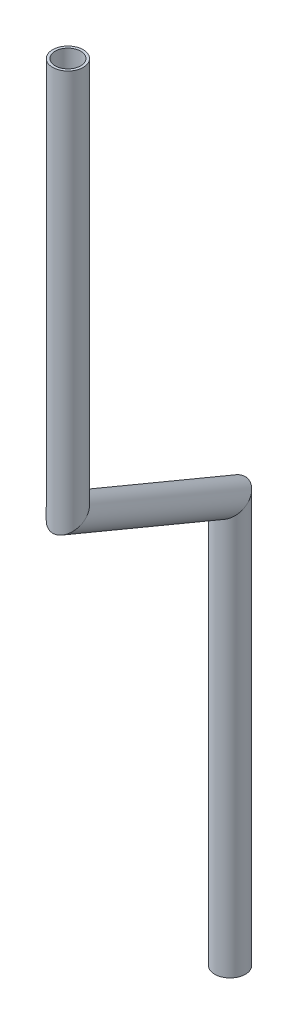
SolidWorks part; units mm, degrees
ref_plane "Front Plane" through (0, 0, 0) normal (0, 0, 1) x (1, 0, 0)
ref_plane "Top Plane" through (0, 0, 0) normal (0, 1, 0) x (1, 0, 0)
ref_plane "Right Plane" through (0, 0, 0) normal (1, 0, 0) x (0, 0, -1)
sketch3d "3DSketch1"
  line L0 (-822.2045, -35.6588, 344.1511) -> (-822.2045, -198.6889, 344.1511)
  line L1 (-822.2045, -198.6889, 344.1511) -> (-824.9646, -229.4117, 274.1878)
  line L2 (-824.9646, -229.4117, 274.1878) -> (-824.9646, -397.5265, 274.1878)
  line L7 (-822.2045, -198.6889, 344.1511) -> (-822.2045, -107.093, 344.1511) construction
  circle A4 centre (-824.9646, -397.5265, 274.1878) radius 5.2832 construction
  circle A7 centre (-822.2045, -35.6588, 344.1511) radius 8.0124 construction
  point P17 (-828.8164, 23.7998, 270.7645)
  point P29 (-824.9646, -402.8097, 274.1878)
  point P31 (-822.2045, -43.6713, 344.1511)
other "Pipe 0.5 SCH 40(1)"
ref_plane "Plane1" through (-822.2045, -35.6588, 344.1511) normal (0, -1, 0) x (1, 0, 0)
sketch "Sketch1" plane through (-822.2045, -35.6588, 344.1511) normal (0, -1, 0) x (1, 0, 0)
  circle A0 centre (0, 0) radius 5.2832
  circle A1 centre (0, 0) radius 6.35
  point P5 (0, 0)
  dimension "In_dia" = 10.5664
  dimension "Out_dia" = 12.7
